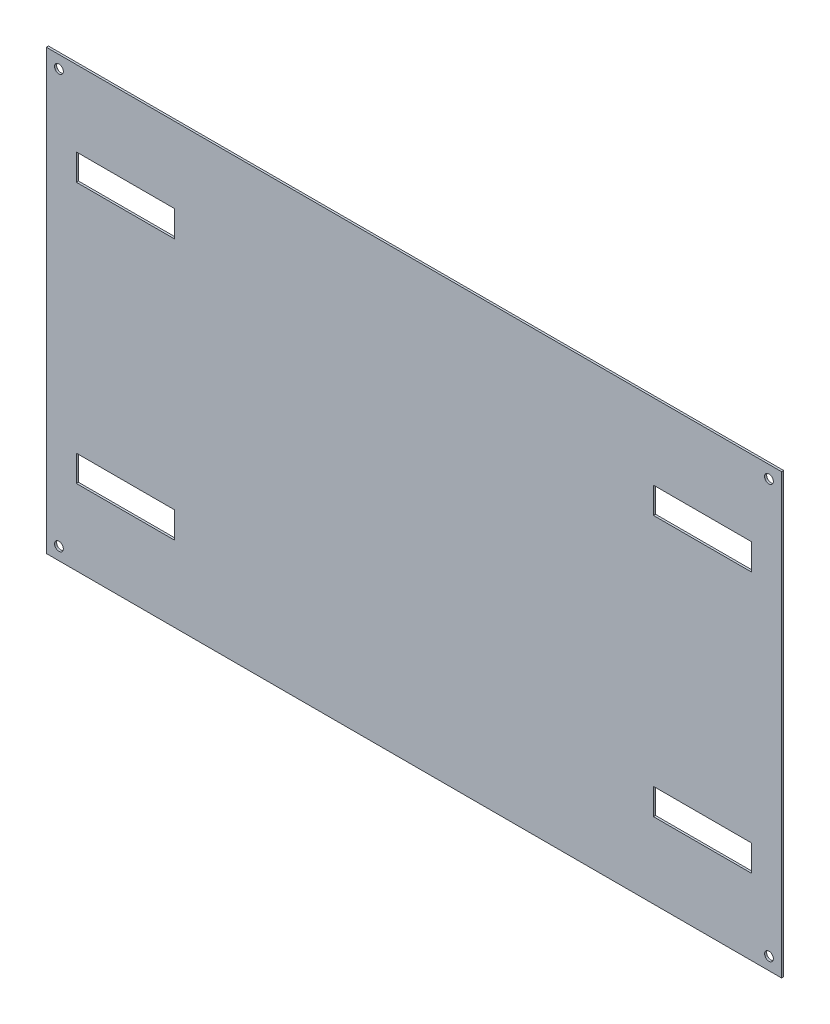
SolidWorks part; units mm, degrees
ref_plane "Front Plane" through (0, 0, 0) normal (0, 0, 1) x (1, 0, 0)
ref_plane "Top Plane" through (0, 0, 0) normal (0, 1, 0) x (1, 0, 0)
ref_plane "Right Plane" through (0, 0, 0) normal (1, 0, 0) x (0, 0, -1)
sketch "Sketch1" plane through (0, 0, 0) normal (0, 0, 1) x (1, 0, 0)
  line L5 (36.0179, 21.4821) -> (0, 0) construction
  line L6 (420, 501) -> (420, 30) construction
  line L10 (87.5, 0) -> (99.5968, 0) construction
  line L23 (0, 0) -> (840, 0)
  line L28 (0, 0) -> (0, 501)
  line L29 (0, 501) -> (840, 501)
  line L30 (57.5, 30) -> (57.5, 57.5) construction
  line L34 (28.75, 28.75) -> (0, 0) construction
  line L41 (840, 443.5) -> (782.5, 501) construction
  line L42 (36.0179, 21.4821) -> (28.75, 28.75) construction
  line L43 (811.25, 472.25) -> (840, 501) construction
  line L44 (28.75, 28.75) -> (0, 0) construction
  line L45 (840, 0) -> (840, 501)
  line L50 (0, 0) -> (57.5, 34.2946) construction
  line L52 (28.75, 28.75) -> (57.5, 57.5) construction
  line L53 (840, 501) -> (670.5, 670.5) construction
  line L54 (169.5, -169.5) -> (111.1958, -227.8042) construction
  line L55 (501, 501) -> (670.5, 670.5) construction
  line L56 (0, 0) -> (169.5, -169.5) construction
  line L57 (803.9821, 479.5179) -> (840, 501) construction
  circle A2 centre (825.625, 486.625) radius 5
  circle A3 centre (14.375, 14.375) radius 5
  circle A4 centre (14.375, 486.625) radius 5
  circle A5 centre (825.625, 14.375) radius 5
extrude "Boss-Extrude1" add sketch "Sketch1" along normal blind 2.4
sketch "Sketch2" plane through (0, 0, 2.4) normal (0, 0, 1) x (1, 0, 0)
  line L0 (114.6787, 0) -> (114.6787, 87.47) construction
  line L1 (0, 0) -> (840, 0) construction
  line L3 (114.6787, 87.47) -> (-111.0913, 87.47) construction
  line L4 (34.32, 116.47) -> (146.32, 116.47)
  line L19 (273.32, 116.47) -> (34.32, 116.47) construction
  line L20 (156.8076, 116.47) -> (156.8076, 70.1372) construction
  line L21 (146.32, 86.47) -> (146.32, 116.47)
  line L22 (146.32, 86.47) -> (34.32, 86.47)
  line L23 (34.32, 116.47) -> (34.32, 86.47)
extrude "Cut-Extrude1" cut sketch "Sketch2" against normal blind 34
ref_plane "Plane1" through (420, 0, 0) normal (1, 0, 0) x (0, 0, -1)
mirror "Mirror1" about plane through (420, 0, 0) normal (1, 0, 0) of "Cut-Extrude1"
ref_plane "Plane2" through (0, 250.5, 0) normal (0, -1, 0) x (-1, 0, 0)
mirror "Mirror2" about plane through (0, 250.5, 0) normal (0, -1, 0) of "Mirror1", "Cut-Extrude1"
